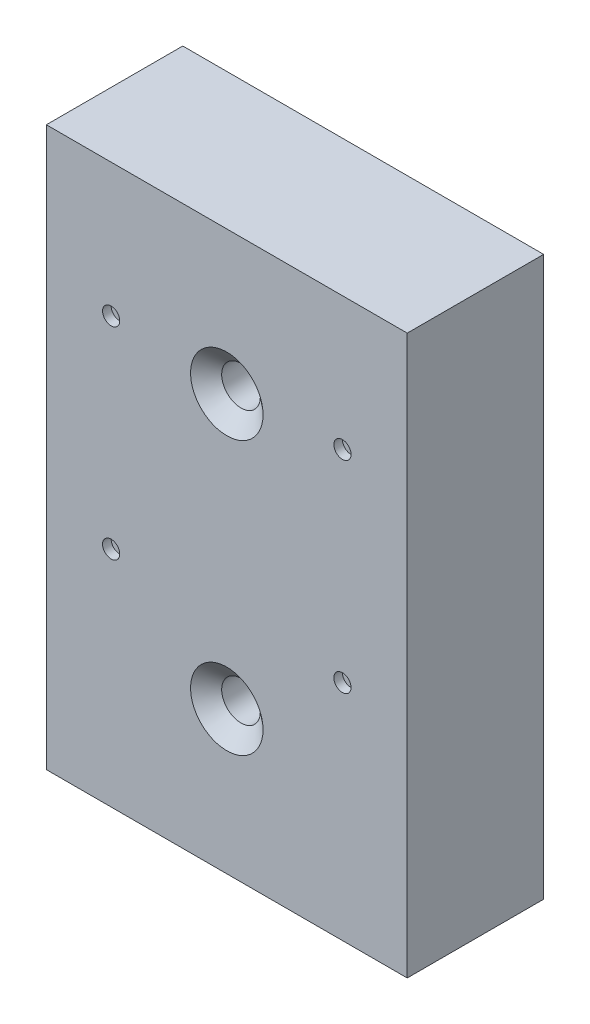
SolidWorks part; units mm, degrees
ref_plane "Front Plane" through (0, 0, 0) normal (0, 0, 1) x (1, 0, 0)
ref_plane "Top Plane" through (0, 0, 0) normal (0, 1, 0) x (1, 0, 0)
ref_plane "Right Plane" through (0, 0, 0) normal (1, 0, 0) x (0, 0, -1)
sketch "Sketch1" plane through (0, 0, 0) normal (0, 0, 1) x (1, 0, 0)
  line L1 (-21, 32.5) -> (21, 32.5)
  line L2 (-21, 32.5) -> (-21, -32.5)
  line L3 (-21, -32.5) -> (21, -32.5)
  line L4 (21, 32.5) -> (21, -32.5)
  line L5 (-21, 32.5) -> (21, -32.5) construction
  line L6 (-21, -32.5) -> (21, 32.5) construction
  point P0 (0, 0)
  dimension "D1" = 65
  dimension "D2" = 42
extrude "Boss-Extrude1" add sketch "Sketch1" along normal blind 15.875
sketch "Sketch2" plane through (0, 0, 15.875) normal (0, 0, 1) x (1, 0, 0)
  line L0 (0, 0) -> (0, -32.5) construction
  line L1 (-21, -32.5) -> (21, -32.5) construction
  circle A0 centre (-13.4595, -6.5) radius 1
  circle A1 centre (-13.4595, 17) radius 1
  circle A4 centre (13.4595, 17) radius 1
  circle A5 centre (13.4595, -6.5) radius 1
  dimension "D2" = 23.5
  dimension "D3" = 2
  dimension "D1" = 26
extrude "Cut-Extrude1" cut sketch "Sketch2" against normal blind 1 and the other way through all
hole_wizard "CSK for #8 Flat Head Machine Screw (100)1" positions "Sketch4" profile "Sketch3" countersink size "#8" standard "ANSI Inch" end condition through all
sketch "Sketch4" plane through (0, 0, 15.875) normal (0, 0, 1) x (1, 0, 0)
  line L0 (0, 0) -> (-21, 0) construction
  line L1 (-21, 32.5) -> (-21, -32.5) construction
  line L4 (0, 32.5) -> (0, -32.5) construction
  line L5 (21, 32.5) -> (-21, 32.5) construction
  line L6 (-21, -32.5) -> (21, -32.5) construction
  point P0 (0, 15.875)
  point P17 (0, -15.875)
  dimension "D1" = 31.75
sketch "Sketch3" plane through (0, 15.875, 15.875) normal (1, 0, 0) x (0, -1, 0)
  line L0 (0, 0) -> (0, 15.875)
  line L1 (0, 15.875) -> (2.2479, 15.875)
  line L2 (2.2479, 15.875) -> (2.2479, 1.6518)
  line L3 (2.2479, 1.6518) -> (4.2164, 0)
  line L5 (4.2164, 0) -> (0, 0)
  line L6 (-2.2479, 1.6518) -> (-4.2164, 0) construction
  line L11 (0, -6.35) -> (0, 107.95) construction
  dimension "Thru Hole Dia." = 4.4958
  dimension "Thru Hole Depth" = 15.875
  dimension "Near C'Sink Dia." = 8.4328
  dimension "Near C'Sink Angle" = 100
